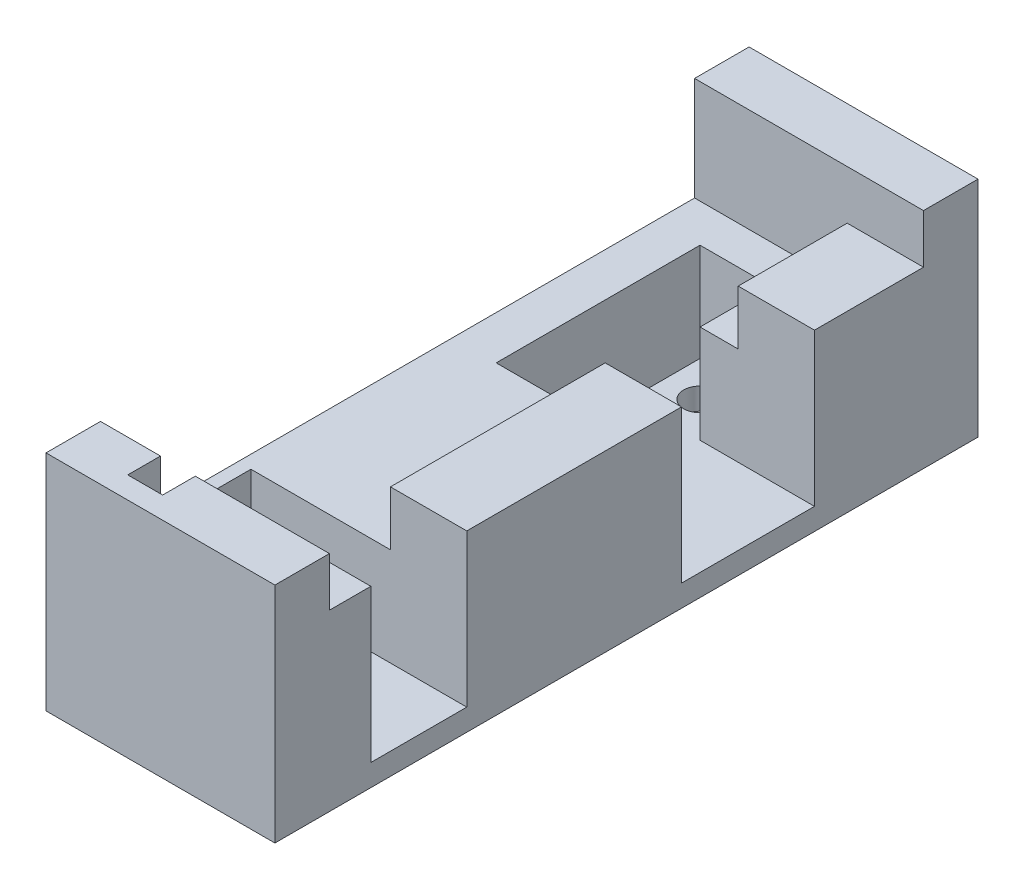
SolidWorks part; units mm, degrees
ref_plane "Front Plane" through (0, 0, 0) normal (0, 0, 1) x (1, 0, 0)
ref_plane "Top Plane" through (0, 0, 0) normal (0, 1, 0) x (1, 0, 0)
ref_plane "Right Plane" through (0, 0, 0) normal (1, 0, 0) x (0, 0, -1)
sketch "Sketch1" plane through (0, 0, 0) normal (0, 1, 0) x (1, 0, 0)
  line L0 (0, 0) -> (-7, 0)
  line L1 (0, 0) -> (0, -10)
  line L2 (0, -10) -> (0, -22.2) construction
  line L3 (0, -22.2) -> (0, -41.9)
  line L4 (0, -41.9) -> (-5.8, -41.9)
  line L5 (-5.8, -41.9) -> (-5.8, -50.7) construction
  line L6 (-5.8, -50.7) -> (0, -50.7)
  line L7 (0, -50.7) -> (0, -54.5)
  line L8 (0, -54.5) -> (-13.5779, -54.5)
  line L9 (-7, 0) -> (-21, 0)
  line L10 (-21, 0) -> (-21, -54.5)
  line L11 (-21, -54.5) -> (-13.5779, -54.5)
  line L12 (0, -10) -> (-10.5, -10)
  line L13 (-17, -10) -> (-17, -22.2)
  line L14 (-17, -22.2) -> (0, -22.2)
  line L15 (-5.8, -41.9) -> (-19.8, -41.9)
  line L16 (-19.8, -41.9) -> (-19.8, -50.7)
  line L17 (-19.8, -50.7) -> (-5.8, -50.7)
  line L18 (-17, -10) -> (-17, -3.5)
  line L19 (-17, -3.5) -> (-10.5, -3.5)
  line L20 (-10.5, -3.5) -> (-10.5, -10)
  point P13 (0, 0)
  dimension "D1" = 7
  dimension "D2" = 10
  dimension "D3" = 12.2
  dimension "D4" = 19.7
  dimension "D5" = 8.8
  dimension "D6" = 5.8
  dimension "D7" = 54.5
  dimension "D8" = 21
  dimension "D9" = 17
  dimension "D10" = 14
  dimension "D11" = 6.5
  dimension "D12" = 6.5
extrude "Boss-Extrude2" add sketch "Sketch1" along normal blind 14
sketch "Sketch3" plane through (0, 0, 0) normal (0, 1, 0) x (1, 0, 0)
  line L0 (-10.5, -3.5) -> (-10.5, -10) construction
  line L1 (-21, 0) -> (0, 0)
  line L2 (-21, 0) -> (-21, -54.5)
  line L3 (-21, -54.5) -> (0, -54.5)
  line L4 (0, 0) -> (0, -54.5)
  line L5 (-17, -3.5) -> (-10.5, -3.5) construction
  line L6 (-10.5, -3.5) -> (-10.5, -10) construction
  line L7 (-17, -3.5) -> (-10.5, -3.5) construction
  line L8 (-17, -3.5) -> (-10.5, -10) construction
  line L9 (-10.5, -10) -> (-10.5, -3.5) construction
  line L10 (-10.5, -3.5) -> (-17, -10) construction
  line L11 (-17, -22.2) -> (-17, -3.5) construction
  circle A0 centre (-13.75, -6.75) radius 1.5
  dimension "D1" = 3
extrude "Boss-Extrude3" add sketch "Sketch3" against normal blind 2
sketch "Sketch4" plane through (0, 14, 0) normal (0, 1, 0) x (1, 0, 0)
  line L0 (-21, -54.5) -> (0, -54.5) construction
  line L1 (-21, 0) -> (-7, 0)
  line L2 (-21, 0) -> (-21, -54.5)
  line L3 (-21, -54.5) -> (-7, -54.5)
  line L4 (-7, 0) -> (-7, -54.5)
  line L5 (0, -10) -> (0, 0) construction
  dimension "D1" = 7
extrude "Cut-Extrude1" cut sketch "Sketch4" against normal blind 5
sketch "Sketch5" plane through (0, 0, 54.5) normal (0, 0, 1) x (1, 0, 0)
  line L0 (-21, 9) -> (-21, -2) construction
  line L1 (0, -2) -> (-21, -2)
  line L2 (0, -2) -> (0, 18.5)
  line L3 (0, 18.5) -> (-21, 18.5)
  line L4 (-21, -2) -> (-21, 18.5)
  line L5 (-12.3, -2) -> (-15.5, -2)
  line L6 (-12.3, 14) -> (-12.3, 18.5)
  line L7 (-12.3, 18.5) -> (-15.5, 18.5)
  line L8 (-15.5, 14) -> (-15.5, 18.5)
  line L9 (-7, 14) -> (0, 14) construction
  line L10 (-7, 14) -> (0, 14) construction
  line L11 (-7, 14) -> (-12.3, 14) construction
  line L12 (-12.3, 14) -> (-15.5, 14)
  line M11 (0, 14) -> (-7, 14)
  line M12 (-7, 14) -> (-7, 9)
  line M13 (-7, 9) -> (-21, 9)
  line M14 (-21, 9) -> (-21, -2)
  line M15 (-21, -2) -> (0, -2)
  line M16 (0, -2) -> (0, 14)
  dimension "D1" = 12.3
  dimension "D2" = 3.2
  dimension "D3" = 4.5
extrude "Boss-Extrude4" add sketch "Sketch5" along normal blind 5 contours L1 M16 M11 M12 M13 M14 M15 | L6 L12 L8 L3 L4 L2 M13 M12 M11
sketch "Sketch7" plane through (0, 0, 0) normal (0, 0, -1) x (-1, 0, 0)
  line L0 (0, 18.5) -> (12.3, 18.5) construction
  line L1 (0, 18.5) -> (12.3, 18.5)
  line L2 (0, 18.5) -> (0, -2)
  line L3 (0, -2) -> (21, -2)
  line L4 (21, -2) -> (21, 18.5)
  line L5 (21, 18.5) -> (12.3, 18.5)
extrude "Boss-Extrude6" add sketch "Sketch7" along normal blind 5
sketch "Sketch8" plane through (-12.3, 0, 0) normal (-1, 0, 0) x (0, 0, 1)
  line L0 (59.5, 14) -> (54.5, 14) construction
  line L1 (59.5, 18.5) -> (57.5, 18.5)
  line L2 (59.5, 18.5) -> (59.5, 14)
  line L3 (59.5, 14) -> (57.5, 14)
  line L4 (57.5, 18.5) -> (57.5, 14)
  line L5 (54.5, 14) -> (54.5, 18.5) construction
  point P9 (54.5, 16.25)
  dimension "D1" = 3
extrude "Boss-Extrude7" add sketch "Sketch8" along normal up to next
